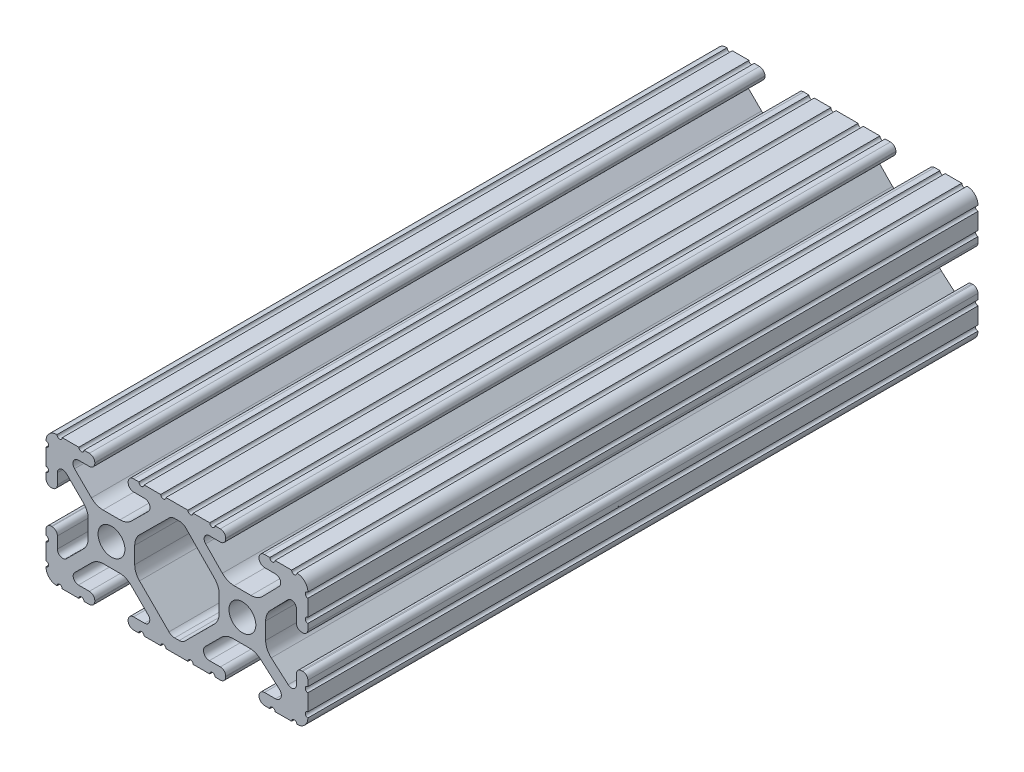
SolidWorks part; units mm, degrees
material "6061 Alloy"
ref_plane "Front Plane" through (0, 0, 0) normal (0, 0, 1) x (1, 0, 0)
ref_plane "Top Plane" through (0, 0, 0) normal (0, 1, 0) x (1, 0, 0)
ref_plane "Right Plane" through (0, 0, 0) normal (1, 0, 0) x (0, 0, -1)
sketch "Sketch1" plane through (0, 0, 0) normal (0, 0, 1) x (1, 0, 0)
  line L0 (-32.9707, 0) -> (32.2708, 0) construction
  line L1 (0, 12.7) -> (0, 0) construction
  line L2 (-12.7, 14.992) -> (-12.7, -12.6999) construction
  line L3 (12.7, 13.9801) -> (12.7, -13.3809) construction
  line L4 (-7.2595, -3.8694) -> (-1.5457, -9.5728)
  line L5 (1.5457, -9.5728) -> (7.2595, -3.8694)
  line L7 (-0.3952, 10.033) -> (0.5515, 10.033)
  line L9 (0.4332, -10.033) -> (-0.4332, -10.033)
  line L12 (8.1915, -1.6223) -> (8.1915, 1.6223)
  line L13 (7.2829, 3.8459) -> (1.6756, 9.5611)
  line L14 (-1.504, 9.5765) -> (-7.252, 3.8768)
  line L15 (-8.1915, 1.6223) -> (-8.1915, -1.6223)
  line L16 (22.2504, 12.7) -> (19.0331, 12.7)
  line L17 (18.0171, 12.7) -> (16.9875, 12.7)
  line L18 (15.9385, 11.651) -> (15.9385, 11.5392)
  line L19 (16.9875, 10.4902) -> (19.1164, 10.4902)
  line L20 (19.8441, 8.7652) -> (16.619, 5.4551)
  line L21 (14.3449, 4.4958) -> (11.0833, 4.4958)
  line L22 (8.817, 5.4472) -> (5.5642, 8.7627)
  line L23 (6.2894, 10.4902) -> (8.4125, 10.4902)
  line L24 (9.4615, 11.5392) -> (9.4615, 11.651)
  line L25 (8.4125, 12.7) -> (7.3829, 12.7)
  line L26 (6.3669, 12.7) -> (3.1496, 12.7)
  line L27 (2.1336, 12.7) -> (-2.1336, 12.7)
  line L28 (-3.1496, 12.7) -> (-6.3669, 12.7)
  line L29 (-7.3829, 12.7) -> (-8.4125, 12.7)
  line L30 (-9.4615, 11.651) -> (-9.4615, 11.5392)
  line L31 (-8.4125, 10.4902) -> (-6.2836, 10.4902)
  line L32 (-5.5326, 8.6661) -> (-8.81, 5.4163)
  line L33 (-11.0455, 4.4958) -> (-14.3545, 4.4958)
  line L34 (-16.59, 5.4163) -> (-19.8674, 8.6661)
  line L35 (-19.1164, 10.4902) -> (-16.9875, 10.4902)
  line L36 (-15.9385, 11.5392) -> (-15.9385, 11.651)
  line L37 (-16.9875, 12.7) -> (-18.0171, 12.7)
  line L38 (-19.0331, 12.7) -> (-22.2504, 12.7)
  line L39 (-25.4, 9.5504) -> (-25.4, 6.3331)
  line L40 (-25.4, 5.3171) -> (-25.4, 4.2375)
  line L41 (-24.401, 3.2385) -> (-24.2392, 3.2385)
  line L42 (-23.1902, 4.2875) -> (-23.1902, 6.3347)
  line L43 (-21.434, 7.0665) -> (-18.148, 3.8082)
  line L44 (-17.2085, 1.5536) -> (-17.2085, -1.6952)
  line L45 (-18.1405, -3.9423) -> (-21.4316, -7.2274)
  line L46 (-23.1902, -6.498) -> (-23.1902, -4.2875)
  line L47 (-24.2392, -3.2385) -> (-24.351, -3.2385)
  line L48 (-25.4, -4.2875) -> (-25.4, -5.3171)
  line L49 (-25.4, -6.3331) -> (-25.4, -9.5504)
  line L50 (-22.2504, -12.7) -> (-19.0331, -12.7)
  line L51 (-18.0171, -12.7) -> (-16.9875, -12.7)
  line L52 (-15.9384, -11.651) -> (-15.9384, -11.5392)
  line L53 (-16.9875, -10.4902) -> (-19.1164, -10.4902)
  line L54 (-19.8341, -8.7551) -> (-16.4966, -5.4237)
  line L55 (-14.2536, -4.4958) -> (-11.1464, -4.4958)
  line L56 (-8.9034, -5.4237) -> (-5.5659, -8.7551)
  line L57 (-6.2836, -10.4902) -> (-8.4125, -10.4902)
  line L58 (-9.4616, -11.5392) -> (-9.4616, -11.651)
  line L59 (-8.4125, -12.7) -> (-7.3829, -12.7)
  line L60 (-6.3669, -12.7) -> (-3.1496, -12.7)
  line L61 (-2.1336, -12.7) -> (2.1336, -12.7)
  line L62 (3.1496, -12.7) -> (6.3669, -12.7)
  line L63 (7.3829, -12.7) -> (8.4125, -12.7)
  line L64 (9.4616, -11.651) -> (9.4616, -11.5392)
  line L65 (8.4125, -10.4902) -> (6.2894, -10.4902)
  line L66 (5.4807, -8.5353) -> (8.5979, -5.4237)
  line L67 (10.8409, -4.4958) -> (14.1026, -4.4958)
  line L68 (16.1879, -5.2766) -> (19.8682, -8.4822)
  line L69 (19.1164, -10.4902) -> (16.9875, -10.4902)
  line L70 (15.9384, -11.5392) -> (15.9384, -11.651)
  line L71 (16.9875, -12.7) -> (18.0171, -12.7)
  line L72 (19.0331, -12.7) -> (22.2504, -12.7)
  line L73 (25.4, -9.5504) -> (25.4, -6.3331)
  line L74 (25.4, -5.3171) -> (25.4, -4.2375)
  line L75 (24.401, -3.2385) -> (24.1892, -3.2385)
  line L76 (23.1902, -4.2375) -> (23.1902, -6.1559)
  line L77 (21.584, -6.8869) -> (18.2982, -4.025)
  line L78 (17.2085, -1.6308) -> (17.2085, 1.6308)
  line L79 (18.1094, 3.8465) -> (21.5263, 7.3534)
  line L80 (23.1902, 6.6769) -> (23.1902, 4.2375)
  line L81 (24.1892, 3.2385) -> (24.401, 3.2385)
  line L82 (25.4, 4.2375) -> (25.4, 5.3171)
  line L83 (25.4, 6.3332) -> (25.4, 9.5504)
  circle A0 centre (-12.7, 0) radius 2.6035
  circle A1 centre (12.7, 0) radius 2.6035
  arc A2 (-0.3952, 10.033) -> (-1.504, 9.5765) centre (-0.3952, 8.4582) ccw
  arc A3 (0.5515, 10.033) -> (1.6756, 9.5611) centre (0.5515, 8.4582) cw
  arc A4 (-8.1915, -1.6223) -> (-7.2595, -3.8694) centre (-5.0165, -1.6223) ccw
  arc A5 (-0.4332, -10.033) -> (-1.5457, -9.5728) centre (-0.4332, -8.4582) cw
  arc A6 (7.2595, -3.8694) -> (8.1915, -1.6223) centre (5.0165, -1.6223) ccw
  arc A7 (8.1915, 1.6223) -> (7.2829, 3.8459) centre (5.0165, 1.6223) ccw
  arc A8 (0.4332, -10.033) -> (1.5457, -9.5728) centre (0.4332, -8.4582) ccw
  arc A9 (-7.252, 3.8768) -> (-8.1915, 1.6223) centre (-5.0165, 1.6223) ccw
  arc A16 (25.3998, 10.5664) -> (23.2664, 12.6998) centre (23.2918, 10.5918) ccw
  arc A17 (22.2504, 12.7) -> (23.2664, 12.6998) centre (22.7584, 12.7) ccw
  arc A18 (18.0171, 12.7) -> (19.0331, 12.7) centre (18.5251, 12.7) ccw
  arc A19 (16.9875, 12.7) -> (15.9385, 11.651) centre (16.9875, 11.651) ccw
  arc A20 (15.9385, 11.5392) -> (16.9875, 10.4902) centre (16.9875, 11.5392) ccw
  arc A21 (19.8441, 8.7652) -> (19.1164, 10.4902) centre (19.1164, 9.4742) ccw
  arc A22 (14.3449, 4.4958) -> (16.619, 5.4551) centre (14.3449, 7.6708) ccw
  arc A23 (8.817, 5.4472) -> (11.0833, 4.4958) centre (11.0833, 7.6708) ccw
  arc A24 (6.2894, 10.4902) -> (5.5642, 8.7627) centre (6.2894, 9.4742) ccw
  arc A25 (8.4125, 10.4902) -> (9.4615, 11.5392) centre (8.4125, 11.5392) ccw
  arc A26 (9.4615, 11.651) -> (8.4125, 12.7) centre (8.4125, 11.651) ccw
  arc A27 (6.3669, 12.7) -> (7.3829, 12.7) centre (6.8749, 12.7) ccw
  arc A28 (2.1336, 12.7) -> (3.1496, 12.7) centre (2.6416, 12.7) ccw
  arc A29 (-3.1496, 12.7) -> (-2.1336, 12.7) centre (-2.6416, 12.7) ccw
  arc A30 (-7.3829, 12.7) -> (-6.3669, 12.7) centre (-6.8749, 12.7) ccw
  arc A31 (-8.4125, 12.7) -> (-9.4615, 11.651) centre (-8.4125, 11.651) ccw
  arc A32 (-9.4615, 11.5392) -> (-8.4125, 10.4902) centre (-8.4125, 11.5392) ccw
  arc A33 (-5.5326, 8.6661) -> (-6.2836, 10.4902) centre (-6.2836, 9.4235) ccw
  arc A34 (-11.0455, 4.4958) -> (-8.81, 5.4163) centre (-11.0455, 7.6708) ccw
  arc A35 (-16.59, 5.4163) -> (-14.3545, 4.4958) centre (-14.3545, 7.6708) ccw
  arc A36 (-19.1164, 10.4902) -> (-19.8674, 8.6661) centre (-19.1164, 9.4235) ccw
  arc A37 (-16.9875, 10.4902) -> (-15.9385, 11.5392) centre (-16.9875, 11.5392) ccw
  arc A38 (-15.9385, 11.651) -> (-16.9875, 12.7) centre (-16.9875, 11.651) ccw
  arc A39 (-19.0331, 12.7) -> (-18.0171, 12.7) centre (-18.5251, 12.7) ccw
  arc A40 (-23.2664, 12.6998) -> (-22.2504, 12.7) centre (-22.7584, 12.7) ccw
  arc A41 (-23.2664, 12.6998) -> (-25.3998, 10.5664) centre (-23.2918, 10.5918) ccw
  arc A42 (-25.4, 9.5504) -> (-25.3998, 10.5664) centre (-25.4, 10.0584) ccw
  arc A43 (-25.4, 5.3171) -> (-25.4, 6.3331) centre (-25.4, 5.8251) ccw
  arc A44 (-25.4, 4.2375) -> (-24.401, 3.2385) centre (-24.401, 4.2375) ccw
  arc A45 (-24.2392, 3.2385) -> (-23.1902, 4.2875) centre (-24.2392, 4.2875) ccw
  arc A46 (-21.434, 7.0665) -> (-23.1902, 6.3347) centre (-22.1596, 6.3347) ccw
  arc A47 (-17.2085, 1.5536) -> (-18.148, 3.8082) centre (-20.3835, 1.5536) ccw
  arc A48 (-18.1405, -3.9423) -> (-17.2085, -1.6952) centre (-20.3835, -1.6952) ccw
  arc A49 (-23.1902, -6.498) -> (-21.4316, -7.2274) centre (-22.1596, -6.498) ccw
  arc A50 (-23.1902, -4.2875) -> (-24.2392, -3.2385) centre (-24.2392, -4.2875) ccw
  arc A51 (-24.351, -3.2385) -> (-25.4, -4.2875) centre (-24.351, -4.2875) ccw
  arc A52 (-25.4, -6.3331) -> (-25.4, -5.3171) centre (-25.4, -5.8251) ccw
  arc A53 (-25.3998, -10.5664) -> (-25.4, -9.5504) centre (-25.4, -10.0584) ccw
  arc A54 (-25.3998, -10.5664) -> (-23.2664, -12.6998) centre (-23.2918, -10.5918) ccw
  arc A55 (-22.2504, -12.7) -> (-23.2664, -12.6998) centre (-22.7584, -12.7) ccw
  arc A56 (-18.0171, -12.7) -> (-19.0331, -12.7) centre (-18.5251, -12.7) ccw
  arc A57 (-16.9875, -12.7) -> (-15.9384, -11.651) centre (-16.9875, -11.651) ccw
  arc A58 (-15.9384, -11.5392) -> (-16.9875, -10.4902) centre (-16.9875, -11.5392) ccw
  arc A59 (-19.8341, -8.7551) -> (-19.1164, -10.4902) centre (-19.1164, -9.4742) ccw
  arc A60 (-14.2536, -4.4958) -> (-16.4966, -5.4237) centre (-14.2536, -7.6708) ccw
  arc A61 (-8.9034, -5.4237) -> (-11.1464, -4.4958) centre (-11.1464, -7.6708) ccw
  arc A62 (-6.2836, -10.4902) -> (-5.5659, -8.7551) centre (-6.2836, -9.4742) ccw
  arc A63 (-8.4125, -10.4902) -> (-9.4616, -11.5392) centre (-8.4125, -11.5392) ccw
  arc A64 (-9.4616, -11.651) -> (-8.4125, -12.7) centre (-8.4125, -11.651) ccw
  arc A65 (-6.3669, -12.7) -> (-7.3829, -12.7) centre (-6.8749, -12.7) ccw
  arc A66 (-2.1336, -12.7) -> (-3.1496, -12.7) centre (-2.6416, -12.7) ccw
  arc A67 (3.1496, -12.7) -> (2.1336, -12.7) centre (2.6416, -12.7) ccw
  arc A68 (7.3829, -12.7) -> (6.3669, -12.7) centre (6.8749, -12.7) ccw
  arc A69 (8.4125, -12.7) -> (9.4616, -11.651) centre (8.4125, -11.651) ccw
  arc A70 (9.4616, -11.5392) -> (8.4125, -10.4902) centre (8.4125, -11.5392) ccw
  arc A71 (5.4807, -8.5353) -> (6.2894, -10.4902) centre (6.2894, -9.3455) ccw
  arc A72 (10.8409, -4.4958) -> (8.5979, -5.4237) centre (10.8409, -7.6708) ccw
  arc A73 (16.1879, -5.2766) -> (14.1026, -4.4958) centre (14.1026, -7.6708) ccw
  arc A74 (19.1164, -10.4902) -> (19.8682, -8.4822) centre (19.1164, -9.3455) ccw
  arc A75 (16.9875, -10.4902) -> (15.9384, -11.5392) centre (16.9875, -11.5392) ccw
  arc A76 (15.9384, -11.651) -> (16.9875, -12.7) centre (16.9875, -11.651) ccw
  arc A77 (19.0331, -12.7) -> (18.0171, -12.7) centre (18.5251, -12.7) ccw
  arc A78 (23.2664, -12.6998) -> (22.2504, -12.7) centre (22.7584, -12.7) ccw
  arc A79 (23.2664, -12.6998) -> (25.3998, -10.5664) centre (23.2918, -10.5918) ccw
  arc A80 (25.4, -9.5504) -> (25.3998, -10.5664) centre (25.4, -10.0584) ccw
  arc A81 (25.4, -5.3171) -> (25.4, -6.3331) centre (25.4, -5.8251) ccw
  arc A82 (25.4, -4.2375) -> (24.401, -3.2385) centre (24.401, -4.2375) ccw
  arc A83 (24.1892, -3.2385) -> (23.1902, -4.2375) centre (24.1892, -4.2375) ccw
  arc A84 (21.584, -6.8869) -> (23.1902, -6.1559) centre (22.2207, -6.1559) ccw
  arc A85 (17.2085, -1.6308) -> (18.2982, -4.025) centre (20.3835, -1.6308) ccw
  arc A86 (18.1094, 3.8465) -> (17.2085, 1.6308) centre (20.3835, 1.6308) ccw
  arc A87 (23.1902, 6.6769) -> (21.5263, 7.3534) centre (22.2207, 6.6769) ccw
  arc A88 (23.1902, 4.2375) -> (24.1892, 3.2385) centre (24.1892, 4.2375) ccw
  arc A89 (24.401, 3.2385) -> (25.4, 4.2375) centre (24.401, 4.2375) ccw
  arc A90 (25.4, 6.3332) -> (25.4, 5.3171) centre (25.4, 5.8251) ccw
  arc A91 (25.3998, 10.5664) -> (25.4, 9.5504) centre (25.4, 10.0584) ccw
  dimension "D1" = 5.207
  dimension "D6" = 6.477
  dimension "D7" = 14.859
  dimension "D14" = 1.5748
  dimension "D16" = 1.5748
  dimension "D15" = 3.175
  dimension "D2" = 25.4
  dimension "D3" = 50.8
  dimension "D4" = 25.4
  dimension "D5" = 8.2042
  dimension "D8" = 2.2098
  dimension "D9" = 2.2098
  dimension "D10" = 2.2098
  dimension "D11" = 2.2098
  dimension "D12" = 2.2098
  dimension "D13" = 6.477
extrude "Extrude1" add sketch "Sketch1" against normal blind 130
